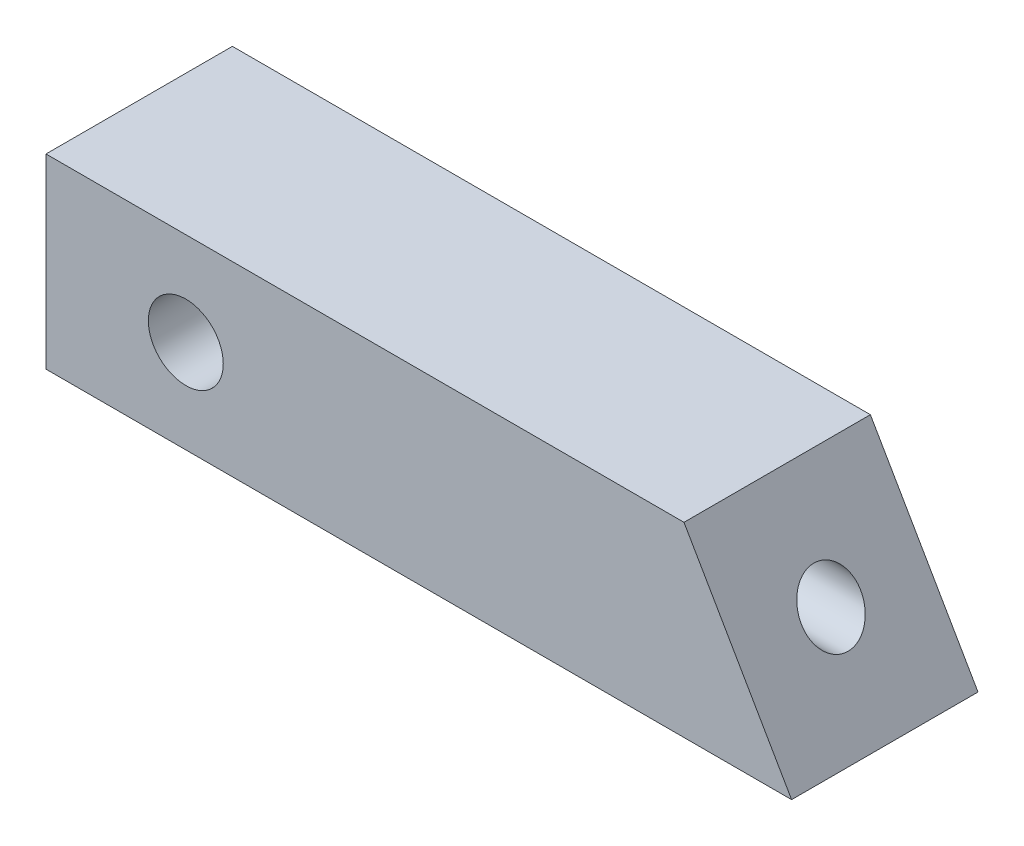
SolidWorks part; units mm, degrees
ref_plane "Front Plane" through (0, 0, 0) normal (0, 0, 1) x (1, 0, 0)
ref_plane "Top Plane" through (0, 0, 0) normal (0, 1, 0) x (1, 0, 0)
ref_plane "Right Plane" through (0, 0, 0) normal (1, 0, 0) x (0, 0, -1)
sketch "Sketch1" plane through (0, 0, 0) normal (1, 0, 0) x (0, 0, -1)
  line L1 (0, 0) -> (12.7, 0)
  line L2 (0, 0) -> (0, 12.7)
  line L3 (0, 12.7) -> (12.7, 12.7)
  line L4 (12.7, 0) -> (12.7, 12.7)
  dimension "D1" = 12.7
  dimension "D2" = 12.7
extrude "Boss-Extrude1" add sketch "Sketch1" along normal blind 50.8
hole_wizard "#10-32 Tapped Hole1" positions "3DSketch1" profile "Sketch2" tap size "#10-32" standard "ANSI Inch"
sketch3d "3DSketch1"
  line L0 (50.8, 6.35, -6.35) -> (50.8, 12.7, -6.35) construction
  line L1 (50.8, 12.7, -12.7) -> (50.8, 12.7, 0) construction
  line L3 (50.8, 0, -12.7) -> (50.8, 12.7, -12.7) construction
  line L4 (50.8, 6.35, -12.7) -> (50.8, 6.35, -6.35) construction
  point P0 (50.8, 6.35, -6.35)
sketch "Sketch2" plane through (50.8, 6.35, -6.35) normal (0, 1, 0) x (0, 0, -1)
  line L0 (0, 0) -> (0, 26.6133)
  line L1 (0, 26.6133) -> (2.0193, 25.4)
  line L2 (2.0193, 25.4) -> (2.0193, 0)
  line L5 (2.0193, 0) -> (0, 0)
  line L10 (0, 26.6133) -> (-2.0193, 25.4) construction
  line L11 (0, -6.35) -> (0, 107.95) construction
  dimension "Tap Drill Dia." = 4.0386
  dimension "Tap Drill Depth" = 25.4
  dimension "Drill Angle" = 118
cosmetic thread "Hole Thread2" parameters "D1"=0, "D2"=5.0386
sketch "Sketch3" plane through (0, 0, 0) normal (0, 0, 1) x (1, 0, 0)
  line L0 (50.8, 0) -> (43.4677, 12.7)
  line L1 (50.8, 12.7) -> (0, 12.7) construction
  line L2 (50.8, 12.7) -> (50.8, 0) construction
  line M4 (50.8, 0) -> (50.8, 12.7)
  line M5 (50.8, 12.7) -> (0, 12.7)
  dimension "D1" = 30
extrude "Cut-Extrude1" cut sketch "Sketch3" against normal through all contours L0 M4 M5
hole_wizard "#10 Clearance Hole1" positions "3DSketch2" profile "Sketch5" hole size "#10" standard "ANSI Inch" end condition through all
sketch3d "3DSketch2"
  line L0 (0, 12.7, 0) -> (0, 0, 0) construction
  line L1 (9.525, 6.35, 0) -> (0, 6.35, 0) construction
  point P0 (9.525, 6.35, 0)
  dimension "D1" = 9.525
sketch "Sketch5" plane through (9.525, 6.35, 0) normal (1, 0, 0) x (0, -1, 0)
  line L0 (0, 0) -> (0, 12.7)
  line L1 (0, 12.7) -> (2.5527, 12.7)
  line L2 (2.5527, 12.7) -> (2.5527, 0)
  line L5 (2.5527, 0) -> (0, 0)
  line L11 (0, -6.35) -> (0, 107.95) construction
  dimension "Thru Hole Dia." = 5.1054
  dimension "Thru Hole Depth" = 12.7
